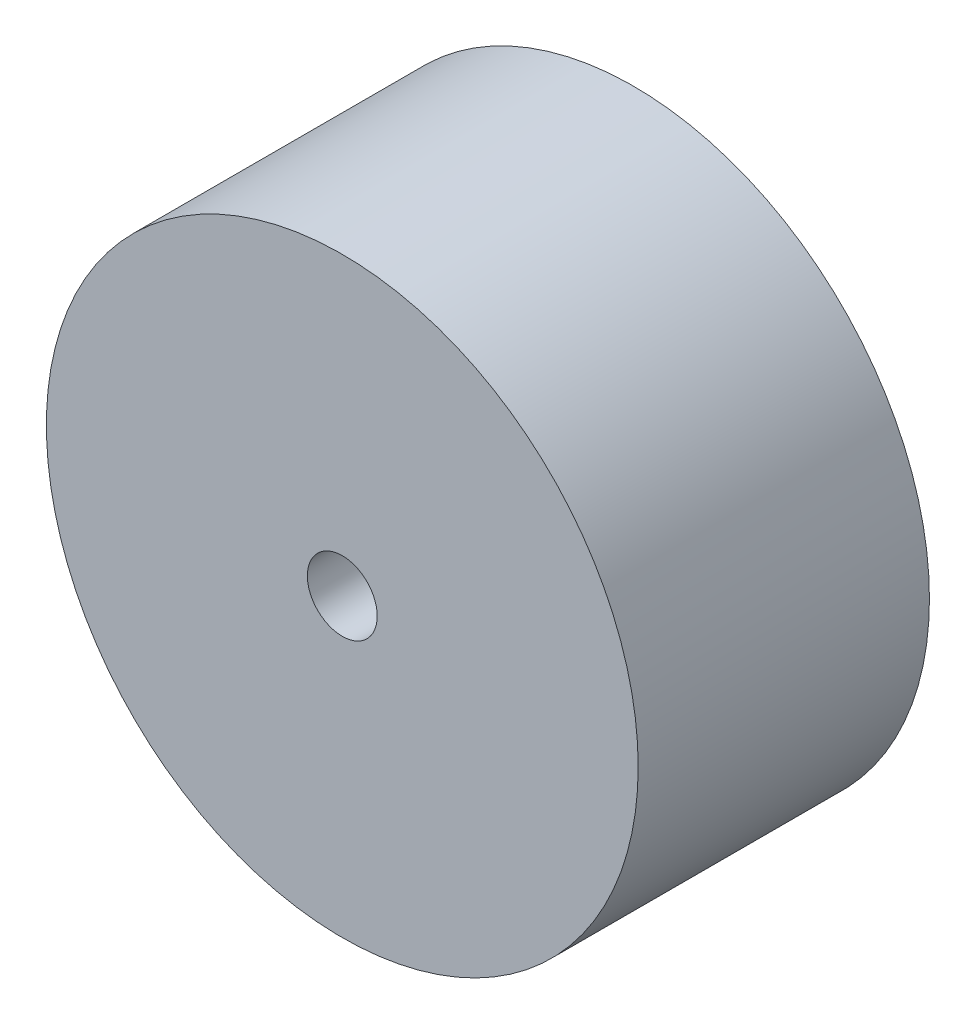
SolidWorks part; units mm, degrees
ref_plane "Front Plane" through (0, 0, 0) normal (0, 0, 1) x (1, 0, 0)
ref_plane "Top Plane" through (0, 0, 0) normal (0, 1, 0) x (1, 0, 0)
ref_plane "Right Plane" through (0, 0, 0) normal (1, 0, 0) x (0, 0, -1)
sketch "Sketch1" plane through (0, 0, 0) normal (0, 0, 1) x (1, 0, 0)
  circle A0 centre (0, 0) radius 50.8
  circle A1 centre (0, 0) radius 6
  dimension "D1" = 101.6
  dimension "D2" = 12
extrude "Boss-Extrude1" add sketch "Sketch1" along normal mid plane 50
